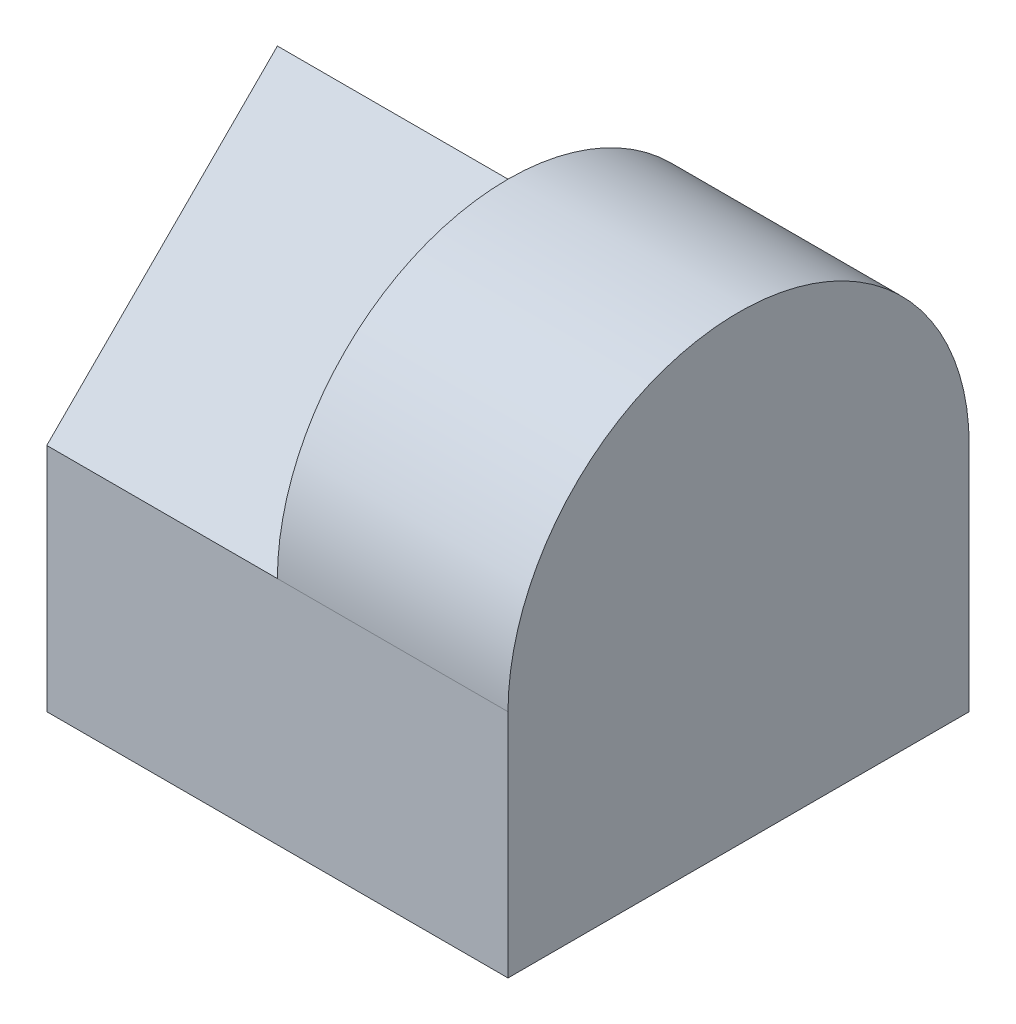
SolidWorks part; units mm, degrees
ref_plane "Front" through (0, 0, 0) normal (0, 0, 1) x (1, 0, 0)
ref_plane "Top" through (0, 0, 0) normal (0, 1, 0) x (1, 0, 0)
ref_plane "Right" through (0, 0, 0) normal (1, 0, 0) x (0, 0, -1)
sketch "Sketch1" plane through (0, 0, 0) normal (0, 1, 0) x (1, 0, 0)
  line L1 (-2, -2) -> (2, -2)
  line L2 (-2, -2) -> (-2, 2)
  line L3 (-2, 2) -> (2, 2)
  line L4 (2, -2) -> (2, 2)
  line L5 (-2, -2) -> (2, 2) construction
  line L6 (-2, 2) -> (2, -2) construction
  point P0 (0, 0)
  dimension "D1" = 4
  dimension "D2" = 4
extrude "Boss-Extrude1" add sketch "Sketch1" along normal blind 4
sketch "Sketch2" plane through (-2, 0, 0) normal (-1, 0, 0) x (0, 0, 1)
  line L0 (2, 2) -> (0, 4)
  line L1 (2, 4) -> (2, 0) construction
  line L2 (-2, 4) -> (2, 4) construction
  line L3 (0, 4) -> (-2, 2)
  line L4 (-2, 4) -> (-2, 0) construction
  line L9 (-2, 0) -> (2, 0)
  line L10 (2, 0) -> (2, 4)
  line L11 (2, 4) -> (-2, 4)
  line L12 (-2, 4) -> (-2, 0)
  line L13 (-2, 0) -> (2, 0)
  line L14 (2, 0) -> (2, 4)
  line L15 (2, 4) -> (-2, 4)
  line L16 (-2, 4) -> (-2, 0)
  line M6 (2, 0) -> (2, 4)
  line M7 (2, 4) -> (-2, 4)
  line M8 (-2, 4) -> (-2, 0)
  dimension "D1" = 0
extrude "Cut-Extrude1" cut sketch "Sketch2" against normal blind 2 contours L3 M7 M8 | L0 M6 M7
sketch "Sketch3" plane through (0, 0, 0) normal (-1, 0, 0) x (0, 0, 1)
  line L0 (0, 4) -> (2, 2) construction
  line L1 (2, 2) -> (2, 4) construction
  line L2 (2, 4) -> (0, 4) construction
  line L3 (-2, 2) -> (0, 4) construction
  line L4 (0, 4) -> (-2, 4) construction
  line L5 (-2, 4) -> (-2, 2) construction
  line L6 (0, 4) -> (2, 2)
  line L7 (2, 2) -> (2, 4)
  line L8 (2, 4) -> (0, 4)
  line L9 (-2, 2) -> (0, 4)
  line L10 (0, 4) -> (-2, 4)
  line L11 (-2, 4) -> (-2, 2)
  arc A0 (-2, 2) -> (2, 2) centre (0, 2) cw
  line M3 (2, 2) -> (2, 4)
  line M4 (2, 4) -> (0, 4)
extrude "Cut-Extrude2" cut sketch "Sketch3" against normal blind 10 contours L11 A0 L10 | A0 M4 M3
